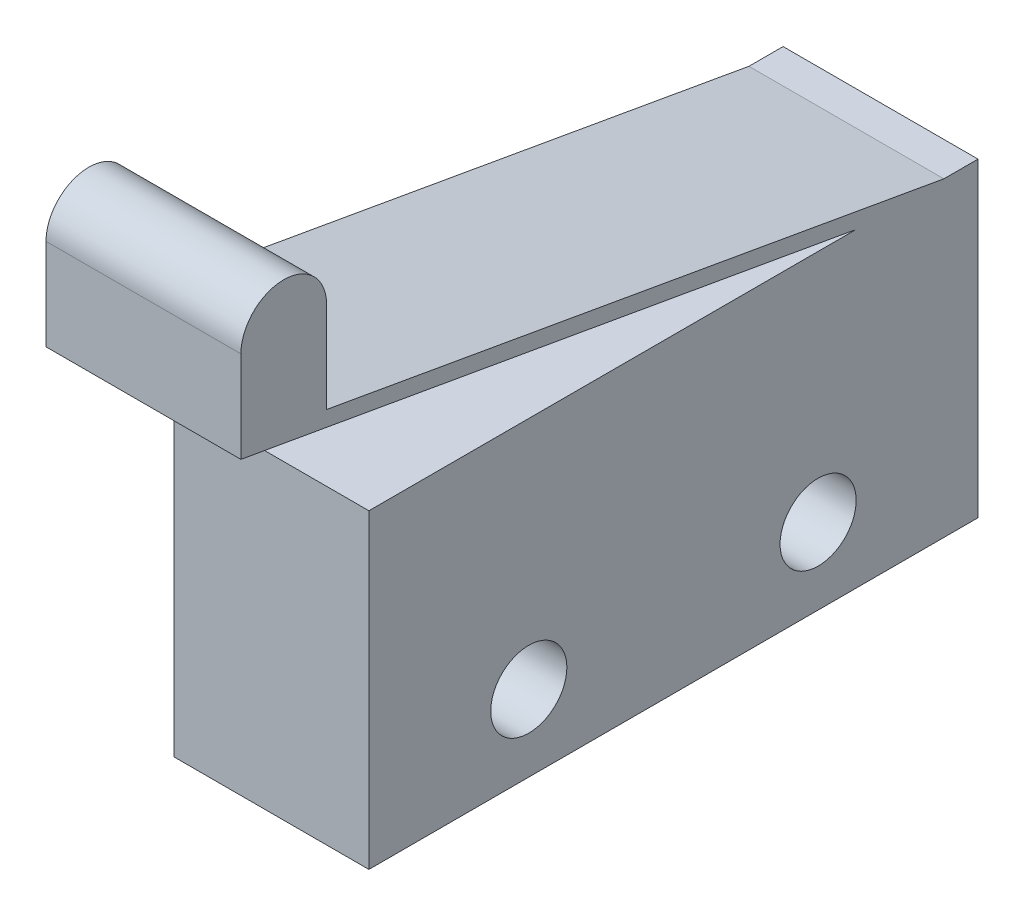
SolidWorks part; units mm, degrees
ref_plane "前视基准面" through (0, 0, 0) normal (0, 0, 1) x (1, 0, 0)
ref_plane "上视基准面" through (0, 0, 0) normal (0, 1, 0) x (1, 0, 0)
ref_plane "右视基准面" through (0, 0, 0) normal (1, 0, 0) x (0, 0, -1)
sketch "草图1" plane through (0, 0, 0) normal (1, 0, 0) x (0, 0, -1)
  line L0 (0, 9.0523) -> (0, -12.104) construction
  line L1 (-10, 10.9708) -> (6, 10.9708)
  line L2 (-10, 10.9708) -> (-10, 0.7708)
  line L3 (-10, 0.7708) -> (10, 0.7708)
  line L4 (10, 10.9708) -> (10, 0.7708)
  line L5 (8.8794, 10.9708) -> (-11.39, 14.5449)
  line L6 (-11.39, 14.5449) -> (-11.39, 17.5331)
  line L8 (-14.2028, 17.5331) -> (-14.2028, 14.5331)
  line L9 (-14.2028, 14.5331) -> (6, 10.9708)
  line L10 (8.8794, 10.9708) -> (10, 10.9708)
  circle A0 centre (-4.75, 3.2708) radius 1.25
  circle A1 centre (4.75, 3.2708) radius 1.25
  arc A2 (-11.39, 17.5331) -> (-14.2028, 17.5331) centre (-12.7964, 17.5331) ccw
  dimension "D3" = 2.5
  dimension "D4" = 9.5
  dimension "D5" = 2.5
  dimension "D10" = 14.2623
  dimension "D11" = 1.4064
  dimension "D1" = 20
  dimension "D2" = 10.2
  dimension "D6" = 0.5
  dimension "D7" = 4
  dimension "D8" = 3
  dimension "D9" = 10
extrude "凸台-拉伸1" add sketch "草图1" along normal blind 6.4
